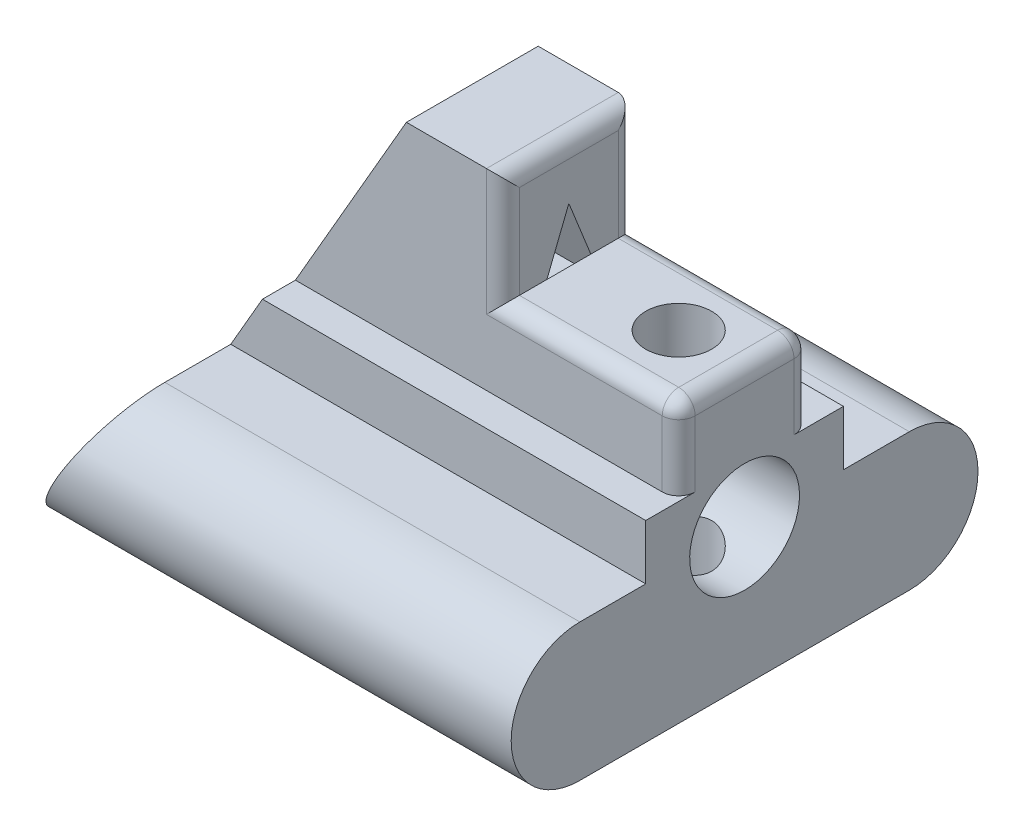
SolidWorks part; units mm, degrees
ref_plane "Front Plane" through (0, 0, 0) normal (0, 0, 1) x (1, 0, 0)
ref_plane "Top Plane" through (0, 0, 0) normal (0, 1, 0) x (1, 0, 0)
ref_plane "Right Plane" through (0, 0, 0) normal (1, 0, 0) x (0, 0, -1)
sketch "Sketch1" plane through (0, 0, 0) normal (1, 0, 0) x (0, 0, -1)
  line L0 (0, 78.7864) -> (0, -32.0071) construction
  line L1 (-30, 0) -> (30, 0)
  line L2 (30, 25) -> (18, 25)
  line L3 (18, 25) -> (18, 35)
  line L4 (18, 35) -> (12, 35)
  line L5 (12, 35) -> (12, 70)
  line L6 (12, 70) -> (-12, 70)
  line L7 (-12, 35) -> (-12, 70)
  line L8 (-18, 35) -> (-12, 35)
  line L9 (-18, 25) -> (-18, 35)
  line L10 (-30, 25) -> (-18, 25)
  line L11 (-6, 45) -> (6, 45)
  line L12 (6, 45) -> (0, 60)
  line L13 (-6, 45) -> (0, 60)
  arc A0 (30, 0) -> (30, 25) centre (30, 12.5) ccw
  arc A1 (-30, 0) -> (-30, 25) centre (-30, 12.5) cw
  circle A2 centre (0, 25) radius 10
  point P16 (0, 70)
  point P19 (0, 0)
  point P25 (0, 45)
  dimension "D2" = 12.5
  dimension "D9" = 20
  dimension "D1" = 30
  dimension "D3" = 12
  dimension "D4" = 6
  dimension "D5" = 25
  dimension "D6" = 10
  dimension "D7" = 24
  dimension "D8" = 35
  dimension "D10" = 25
  dimension "D11" = 6
  dimension "D12" = 15
  dimension "D13" = 45
extrude "Boss-Extrude1" add sketch "Sketch1" along normal blind 90
sketch "Sketch2" plane through (0, 0, 0) normal (0, 0, 1) x (1, 0, 0)
  line L0 (0, 0) -> (40.4145, 70)
  line L1 (90, 70) -> (0, 70) construction
  line L2 (0, 25) -> (0, 0) construction
  line L3 (40.4145, 70) -> (0, 70)
  line L4 (0, 70) -> (0, 0)
  dimension "D1" = 30
extrude "Cut-Extrude1" cut sketch "Sketch2" along normal blind 46 and the other way blind 57
sketch "Sketch3" plane through (0, 70, 0) normal (0, 1, 0) x (1, 0, 0)
  line L0 (90, 12) -> (58, 12)
  line L1 (90, 12) -> (40.4145, 12) construction
  line L2 (58, 12) -> (58, -12)
  line L3 (90, -12) -> (20.2073, -12) construction
  line L4 (58, -12) -> (90, -12)
  line L5 (90, -12) -> (90, 12)
  dimension "D1" = 32
extrude "Cut-Extrude2" cut sketch "Sketch3" against normal blind 20
sketch "Sketch4" plane through (58, 0, 0) normal (1, 0, 0) x (0, 0, -1)
  line L0 (-6, 45) -> (-4, 50)
  line L1 (-4, 50) -> (4, 50)
  line L2 (4, 50) -> (6, 45)
  line L3 (6, 45) -> (-6, 45)
extrude "Boss-Extrude2" add sketch "Sketch4" along normal blind 32
sketch "Sketch5" plane through (0, 50, 0) normal (0, 1, 0) x (1, 0, 0)
  line L0 (90, -12) -> (90, 12) construction
  line L1 (90, 12) -> (20.2073, 12) construction
  circle A0 centre (78, 0) radius 6
  dimension "D1" = 12
  dimension "D2" = 12
  dimension "D3" = 12
extrude "Cut-Extrude3" cut sketch "Sketch5" against normal blind 78
fillet "Fillet3" radius 3 8 edges at (90, 42.5, 12) (90, 42.5, -12) (90, 50, 0) (74, 50, 12) (74, 50, -12) (58, 60, -12) (58, 70, 0) (58, 60, 12)
